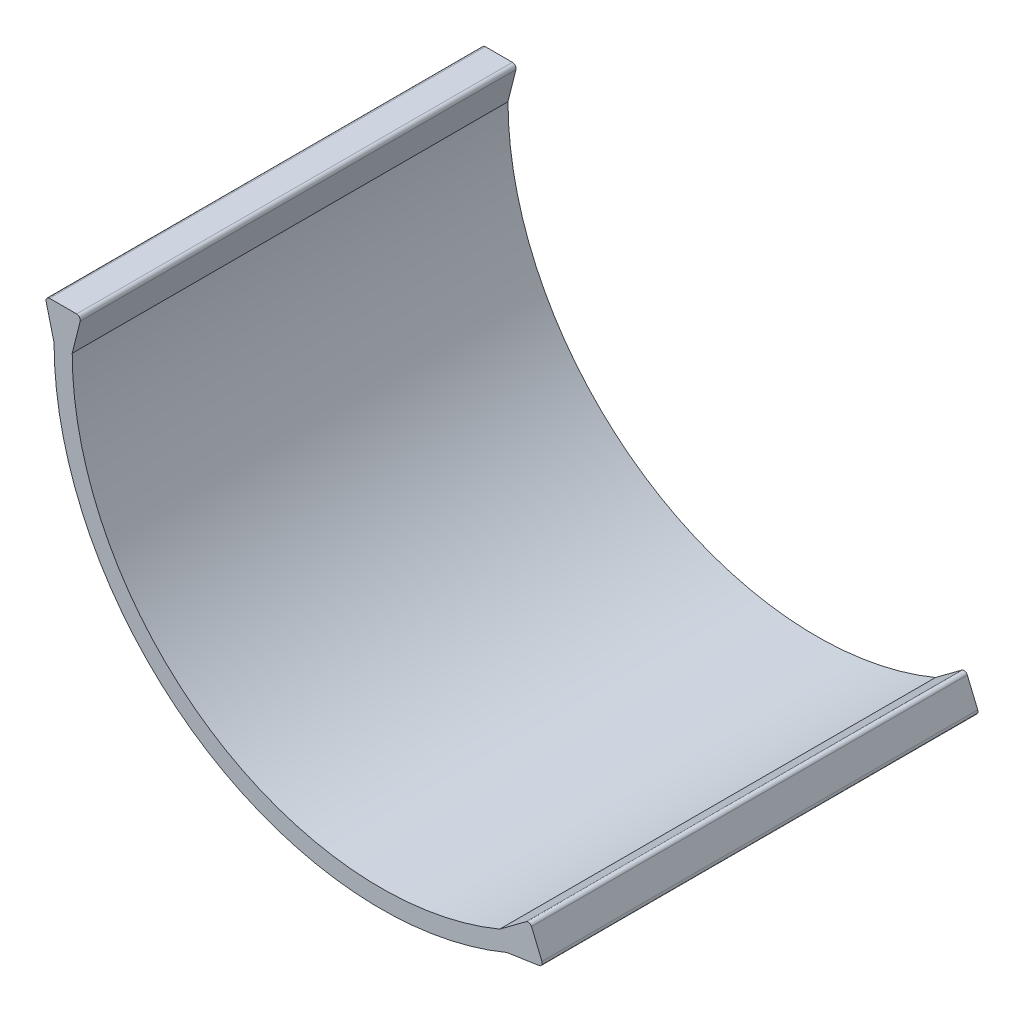
SolidWorks part; units mm, degrees
ref_plane "Front Plane" through (0, 0, 0) normal (0, 0, 1) x (1, 0, 0)
ref_plane "Top Plane" through (0, 0, 0) normal (0, 1, 0) x (1, 0, 0)
ref_plane "Right Plane" through (0, 0, 0) normal (1, 0, 0) x (0, 0, -1)
sketch "Curve" plane through (0, 0, 0) normal (0, 0, 1) x (1, 0, 0)
  line L0 (-85, 0) -> (0, 0) construction
  line L1 (0, 0) -> (32.7154, -78.4519) construction
  line L2 (-68.6173, 0) -> (72.7117, 0) construction
  arc A0 (-85, 0) -> (32.7154, -78.4519) centre (0, 0) ccw
  dimension "D1" = 85
  dimension "D2" = 167.1
extrude "Main Body" add sketch "Curve" along normal blind 120 thin contours A0
sketch "Lock shape" plane through (0, 0, 120) normal (0, 0, 1) x (1, 0, 0)
  line L0 (33.6777, -80.7593) -> (63.9684, -68.1277) construction
  line L1 (32.7154, -78.4519) -> (34.6399, -83.0667) construction
  line L2 (32.7154, -78.4519) -> (39.9556, -73.0605)
  line L3 (41.4758, -73.4777) -> (44.3388, -80.3431)
  line L4 (43.5654, -81.7168) -> (34.6399, -83.0667)
  line L5 (33.6777, -80.7593) -> (32.7154, -78.4519) construction
  line L8 (34.6399, -83.0667) -> (32.7154, -78.4519)
  line L9 (-85, 0) -> (-90, 0)
  line L10 (34.6399, -83.0667) -> (32.7154, -78.4519)
  arc A0 (39.9556, -73.0605) -> (41.4758, -73.4777) centre (40.5529, -73.8626) cw
  arc A1 (44.3388, -80.3431) -> (43.5654, -81.7168) centre (43.4158, -80.728) cw
  arc A4 (-90, 0) -> (34.6399, -83.0667) centre (0, 0) ccw
  arc A5 (-85, 0) -> (32.7154, -78.4519) centre (0, 0) ccw
  point P7 (42.9073, -76.9104)
  point P13 (40.9829, -72.2956)
  point P16 (44.8317, -81.5252)
  dimension "D4" = 1
  dimension "D5" = 1
  dimension "D1" = 10
  dimension "D2" = 10
  dimension "D3" = 90
  dimension "D6" = 0
extrude "Locking Mechanism" add sketch "Lock shape" against normal blind 120
sketch "Lock shape 2" plane through (0, 0, 120) normal (0, 0, 1) x (1, 0, 0)
  line L0 (-87.5, 0) -> (-87.5, 29.5984) construction
  line L1 (-90, 0) -> (-85, 0) construction
  line L2 (-90, 0) -> (-92.1894, 8.7575)
  line L3 (-91.2192, 10) -> (-83.7808, 10)
  line L4 (-82.8106, 8.7575) -> (-85, 0)
  line L9 (34.6399, -83.0667) -> (43.5654, -81.7168)
  line L10 (44.3388, -80.3431) -> (41.4758, -73.4777)
  line L11 (39.9556, -73.0605) -> (32.7154, -78.4519)
  line L12 (-85, 0) -> (-90, 0)
  line L16 (-85, 0) -> (-90, 0)
  arc A0 (-83.7808, 10) -> (-82.8106, 8.7575) centre (-83.7808, 9) cw
  arc A1 (-91.2192, 10) -> (-92.1894, 8.7575) centre (-91.2192, 9) ccw
  arc A6 (-90, 0) -> (34.6399, -83.0667) centre (0, 0) ccw
  arc A7 (43.5654, -81.7168) -> (44.3388, -80.3431) centre (43.4158, -80.728) ccw
  arc A8 (41.4758, -73.4777) -> (39.9556, -73.0605) centre (40.5529, -73.8626) ccw
  arc A9 (-85, 0) -> (32.7154, -78.4519) centre (0, 0) ccw
  point P12 (-82.5, 10)
  point P15 (-92.5, 10)
  dimension "D3" = 1
  dimension "D1" = 10
  dimension "D2" = 10
  dimension "D4" = 0
extrude "Locking Mechanism 2" add sketch "Lock shape 2" against normal blind 120
ref_plane "Plane1" through (-26.1423, -39.2259, 0) normal (-0.5546, -0.8321, 0) x (-0.8321, 0.5546, 0)
sketch "Sketch5" plane through (-26.1423, -39.2259, 0) normal (-0.5546, -0.8321, 0) x (-0.8321, 0.5546, 0)
  line L0 (-70.7312, -120) -> (70.7312, -120) construction
  line L1 (-70.7312, -120) -> (-70.7312, 0) construction
  line L2 (-55.7023, -110) -> (69.7348, -110) construction
  circle A0 centre (-55.7023, -110) radius 0.5
  dimension "D1" = 1
  dimension "D2" = 10
  dimension "D3" = 15.0289
curve "Curve1"
